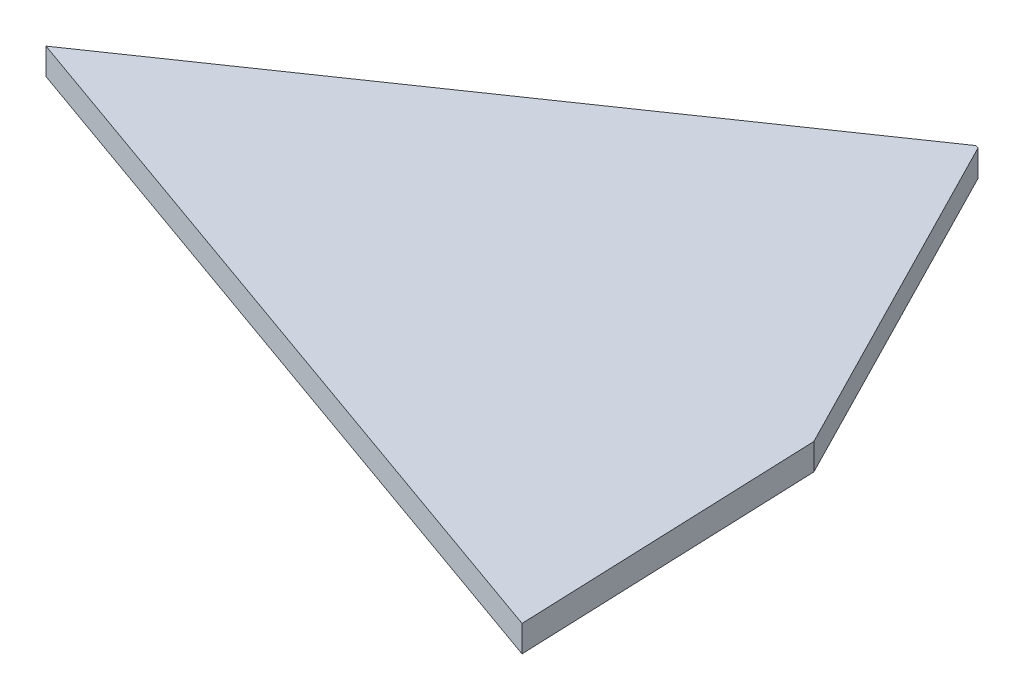
SolidWorks part; units mm, degrees
ref_plane "Plan de face" through (0, 0, 0) normal (0, 0, 1) x (1, 0, 0)
ref_plane "Plan de dessus" through (0, 0, 0) normal (0, 1, 0) x (1, 0, 0)
ref_plane "Plan de droite" through (0, 0, 0) normal (1, 0, 0) x (0, 0, -1)
sketch "Esquisse1" plane through (0, 0, 0) normal (0, 1, 0) x (1, 0, 0)
  line L0 (41.761, 28.7042) -> (0, 0)
  line L1 (0, 0) -> (55.9163, -19.8474)
  line L2 (55.9163, -19.8474) -> (55.0308, 3.1466)
  line L3 (55.0308, 3.1466) -> (41.9926, 28.622)
  line L4 (41.9926, 28.622) -> (41.761, 28.7042)
  point P5 (0, 0)
extrude "Boss.-Extru.1" add sketch "Esquisse1" along normal blind 2
